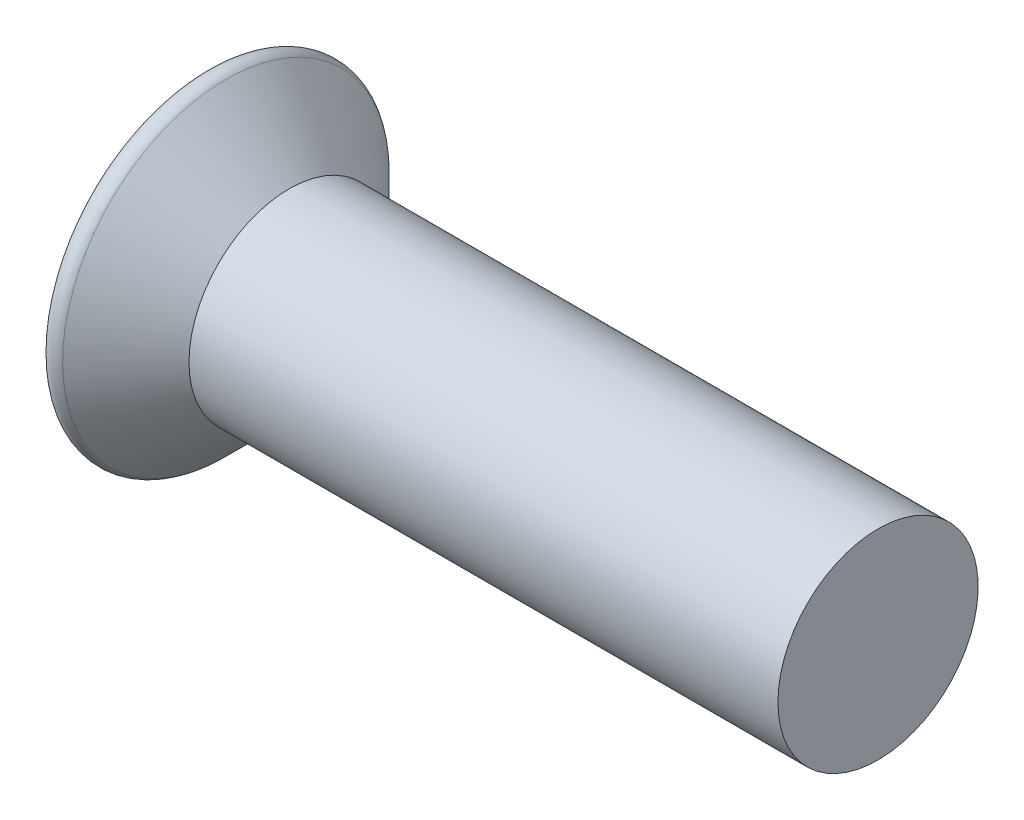
SolidWorks part; units mm, degrees
ref_plane "前视基准面" through (0, 0, 0) normal (0, 0, 1) x (1, 0, 0)
ref_plane "上视基准面" through (0, 0, 0) normal (0, 1, 0) x (1, 0, 0)
ref_plane "右视基准面" through (0, 0, 0) normal (1, 0, 0) x (0, 0, -1)
other "Configuration Table"
sketch "草图1" plane through (0, 0, 0) normal (0, 0, 1) x (1, 0, 0)
  line L0 (-0.7071, 0) -> (5, 0)
  line L1 (-0.7071, 1.5571) -> (-0.7071, 0)
  line L2 (0, 0.85) -> (5, 0.85)
  line L3 (5, 0) -> (5, 0.85)
  line L4 (0, 0.85) -> (-0.7071, 1.5571)
  dimension "D4" = 1
revolve "旋转2" add sketch "草图1" angle 360 about L0
sketch "草图2" plane through (-0.7071, 0, 0) normal (-1, 0, 0) x (0, 0, 1)
  line L0 (-0.1163, 0.9849) -> (0.1163, -0.9849) construction
  line L1 (-0.9849, -0.1163) -> (0.9849, -0.1163)
  line L2 (-0.9849, -0.1163) -> (-0.9849, 0.1163)
  line L3 (-0.9849, 0.1163) -> (0.9849, 0.1163)
  line L4 (0.9849, -0.1163) -> (0.9849, 0.1163)
  line L5 (-0.9849, -0.1163) -> (0.9849, 0.1163) construction
  line L6 (-0.9849, 0.1163) -> (0.9849, -0.1163) construction
  line L7 (0.1163, 0.9849) -> (-0.1163, -0.9849) construction
  line L8 (-0.1163, 0.9849) -> (0.1163, 0.9849)
  line L9 (-0.1163, 0.9849) -> (-0.1163, -0.9849)
  line L10 (-0.1163, -0.9849) -> (0.1163, -0.9849)
  line L11 (0.1163, 0.9849) -> (0.1163, -0.9849)
  point P0 (0, 0)
  point P8 (0, 0)
  point P13 (0, 0)
  dimension "D1" = 2
extrude "切除-拉伸1" cut sketch "草图2" against normal blind 0.2 contours L11 L1 L9 L10 | L3 L11 L1 L4 | L11 L3 L9 L1 | L11 L8 L9 L3 | L9 L3 L2 L1
fillet "圆角1" radius 0.1 1 edges at (-0.7071, 0, 1.5571)
